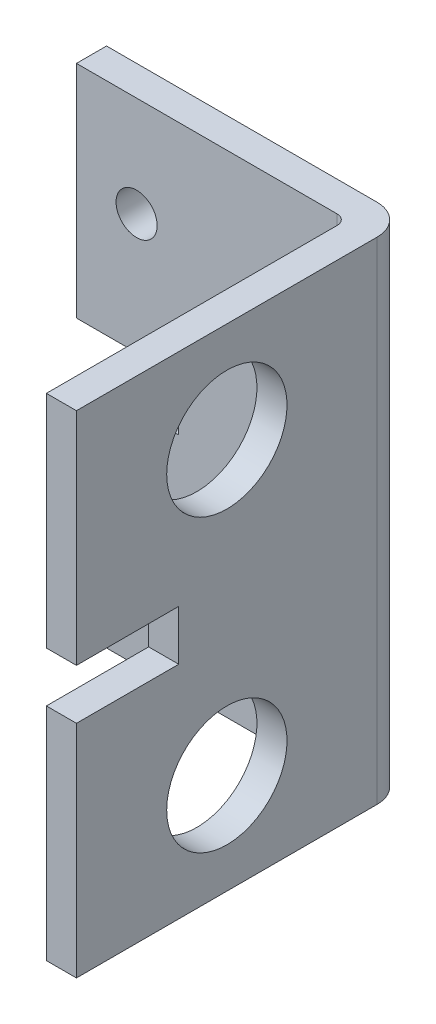
SolidWorks part; units mm, degrees
ref_plane "Front Plane" through (0, 0, 0) normal (0, 0, 1) x (1, 0, 0)
ref_plane "Top Plane" through (0, 0, 0) normal (0, 1, 0) x (1, 0, 0)
ref_plane "Right Plane" through (0, 0, 0) normal (1, 0, 0) x (0, 0, -1)
sketch "Sketch2" plane through (0, 0, 0) normal (0, 0, 1) x (1, 0, 0)
  line L1 (0, 0) -> (27, 0)
  line L2 (0, 0) -> (0, 49)
  line L3 (0, 49) -> (27, 49)
  line L4 (27, 0) -> (27, 49)
  line L5 (6, 39) -> (21, 39) construction
  line L6 (6, 39) -> (6, 10) construction
  line L7 (6, 10) -> (21, 10) construction
  line L8 (21, 39) -> (21, 10) construction
  circle A0 centre (6, 39) radius 2.05
  circle A1 centre (21, 39) radius 2.05
  circle A2 centre (6, 10) radius 2.05
  circle A3 centre (21, 10) radius 2.05
  point P13 (13.5, 10)
  point P14 (13.5, 0)
  point P15 (6, 24.5)
  point P16 (0, 24.5)
  dimension "D1" = 4.1
  dimension "D2" = 15
  dimension "D3" = 29
  dimension "D4" = 10
  dimension "D5" = 6
extrude "Boss-Extrude1" add sketch "Sketch2" along normal blind 3
sketch "Sketch4" plane through (0, 49, 0) normal (0, 1, 0) x (1, 0, 0)
  line L0 (27, 0) -> (0, 0) construction
  line L2 (30, -3) -> (30, -33)
  line L3 (30, -33) -> (27, -33)
  line L5 (27, -3) -> (27, 0) construction
  line L8 (27, -33) -> (27, 0)
  arc A0 (27, 0) -> (30, -3) centre (27, -3) cw
  dimension "D1" = 30
extrude "Boss-Extrude2" add sketch "Sketch4" against normal up to surface (49 mm away) up to face at (13.5, 0, 1.5)
sketch "Sketch5" plane through (27, 0, 0) normal (-1, 0, 0) x (0, 0, 1)
  line L1 (33, 0) -> (3, 0) construction
  line L2 (33, 0) -> (33, 49) construction
  circle A0 centre (18, 39) radius 6
  circle A1 centre (18, 10) radius 6
  dimension "D1" = 12
  dimension "D2" = 29
  dimension "D3" = 10
  dimension "D4" = 15
extrude "Cut-Extrude1" cut sketch "Sketch5" against normal through all
fillet "Fillet1" radius 1 1 edges at (27, 24.5, 3)
sketch "Sketch6" plane through (0, 0, 3) normal (0, 0, 1) x (1, 0, 0)
  line L0 (0, 49) -> (0, 0) construction
  line L1 (-3, 27) -> (10.2, 27)
  line L2 (-3, 27) -> (-3, 22)
  line L3 (-3, 22) -> (10.2, 22)
  line L4 (10.2, 27) -> (10.2, 22)
  point P8 (0, 24.5)
  point P9 (-3, 24.5)
  dimension "D1" = 5
  dimension "D2" = 3
  dimension "D3" = 10.2
extrude "Cut-Extrude2" cut sketch "Sketch6" against normal through all
sketch "Sketch7" plane through (27, 0, 0) normal (-1, 0, 0) x (0, 0, 1)
  line L0 (33, 0) -> (33, 49) construction
  line L1 (33, 27) -> (22.8, 27)
  line L2 (33, 27) -> (33, 22)
  line L3 (33, 22) -> (22.8, 22)
  line L4 (22.8, 27) -> (22.8, 22)
  line L5 (0, 27) -> (3, 27) construction
  line L6 (3, 22) -> (0, 22) construction
  dimension "D1" = 10.2
extrude "Cut-Extrude3" cut sketch "Sketch7" against normal through all and the other way through all
